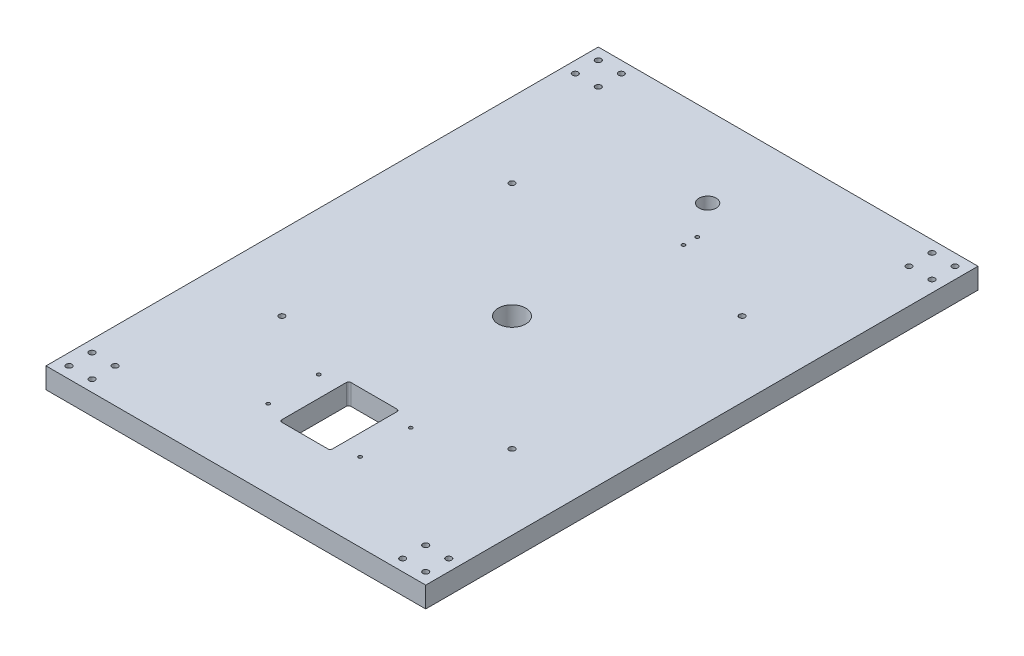
SolidWorks part; units mm, degrees
ref_plane "Front Plane" through (0, 0, 0) normal (0, 0, 1) x (1, 0, 0)
ref_plane "Top Plane" through (0, 0, 0) normal (0, 1, 0) x (1, 0, 0)
ref_plane "Right Plane" through (0, 0, 0) normal (1, 0, 0) x (0, 0, -1)
sketch "Sketch1" plane through (0, 0, 0) normal (0, 1, 0) x (1, 0, 0)
  line L0 (0, 240) -> (330, 240) construction
  line L1 (0, 0) -> (330, 0)
  line L2 (0, 0) -> (0, 480)
  line L3 (0, 480) -> (330, 480)
  line L4 (330, 0) -> (330, 480)
  line L5 (165, 480) -> (165, 0) construction
  line L7 (145, 60) -> (185, 60)
  line L8 (143, 62) -> (143, 118)
  line L9 (145, 120) -> (185, 120)
  line L10 (187, 62) -> (187, 118)
  circle A0 centre (10, 10) radius 2.5
  circle A1 centre (30, 10) radius 2.5
  circle A2 centre (10, 30) radius 2.5
  circle A3 centre (30, 30) radius 2.5
  circle A4 centre (320, 30) radius 2.5
  circle A5 centre (320, 10) radius 2.5
  circle A6 centre (300, 10) radius 2.5
  circle A7 centre (300, 30) radius 2.5
  circle A8 centre (300, 470) radius 2.5
  circle A9 centre (320, 470) radius 2.5
  circle A10 centre (320, 450) radius 2.5
  circle A11 centre (300, 450) radius 2.5
  circle A12 centre (30, 470) radius 2.5
  circle A13 centre (10, 470) radius 2.5
  circle A14 centre (10, 450) radius 2.5
  circle A15 centre (30, 450) radius 2.5
  circle A16 centre (65, 140) radius 2.5
  circle A17 centre (65, 340) radius 2.5
  circle A18 centre (265, 140) radius 2.5
  circle A19 centre (265, 340) radius 2.5
  circle A20 centre (165, 240) radius 12
  arc A21 (145, 60) -> (143, 62) centre (145, 62) cw
  arc A22 (185, 60) -> (187, 62) centre (185, 62) ccw
  arc A23 (185, 120) -> (187, 118) centre (185, 118) cw
  arc A24 (143, 118) -> (145, 120) centre (145, 118) cw
  circle A25 centre (125, 112) radius 1.5
  circle A26 centre (125, 68) radius 1.5
  circle A27 centre (205, 112) radius 1.5
  circle A28 centre (205, 68) radius 1.5
  circle A29 centre (186, 368) radius 1.5
  circle A30 centre (186, 380) radius 1.5
  circle A31 centre (165, 410) radius 7.5
  point P55 (165, 60)
  point P60 (187, 60)
  point P63 (187, 120)
  point P66 (143, 120)
  point P71 (143, 90)
  dimension "D3" = 5
  dimension "D9" = 5
  dimension "D12" = 24
  dimension "D16" = 2
  dimension "D19" = 3
  dimension "D22" = 3
  dimension "D26" = 15
  dimension "D1" = 330
  dimension "D2" = 480
  dimension "D4" = 20
  dimension "D5" = 20
  dimension "D6" = 20
  dimension "D7" = 10
  dimension "D8" = 10
  dimension "D10" = 100
  dimension "D11" = 100
  dimension "D13" = 44
  dimension "D14" = 60
  dimension "D15" = 60
  dimension "D17" = 40
  dimension "D18" = 44
  dimension "D20" = 22
  dimension "D21" = 12
  dimension "D23" = 21
  dimension "D24" = 100
  dimension "D25" = 70
extrude "Boss-Extrude1" add sketch "Sketch1" along normal blind 18
